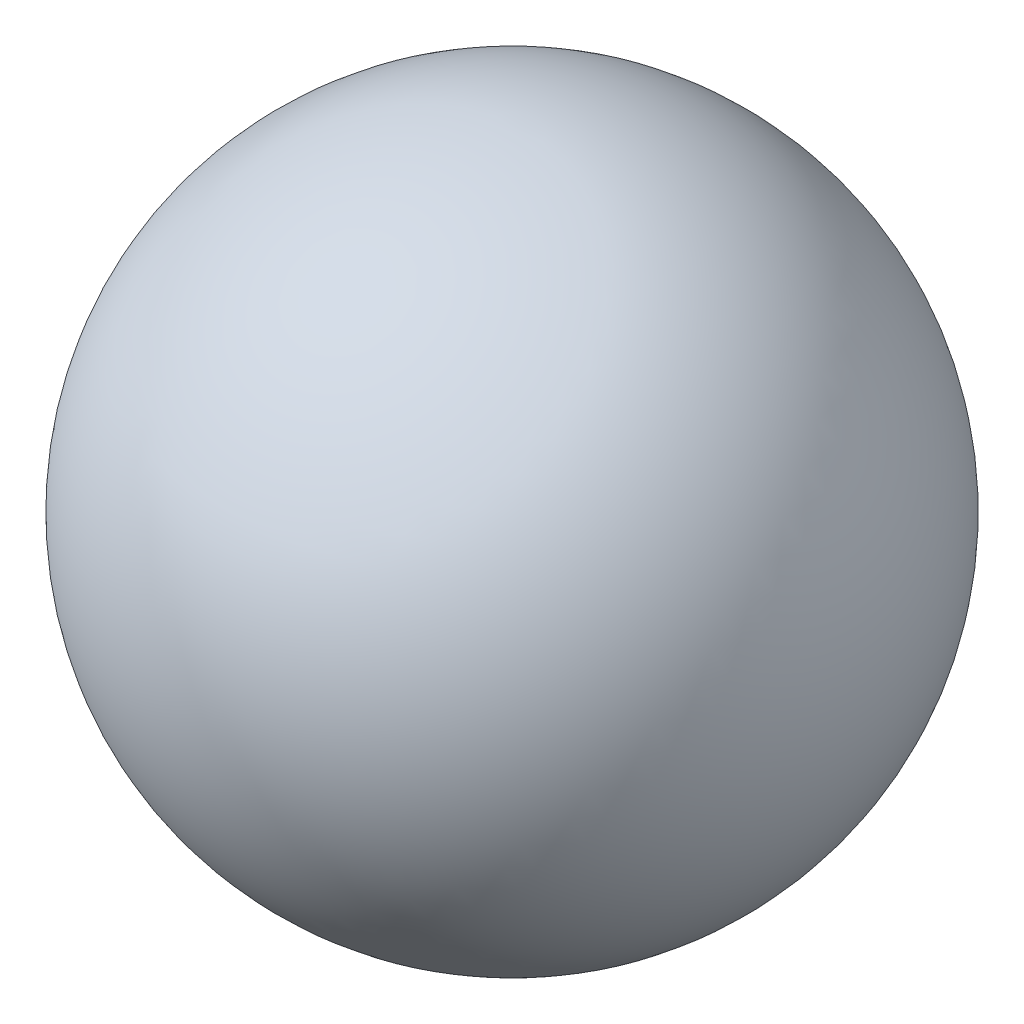
SolidWorks part; units mm, degrees
ref_plane "Front Plane" through (0, 0, 0) normal (0, 0, 1) x (1, 0, 0)
ref_plane "Top Plane" through (0, 0, 0) normal (0, 1, 0) x (1, 0, 0)
ref_plane "Right Plane" through (0, 0, 0) normal (1, 0, 0) x (0, 0, -1)
sketch "Sketch1" plane through (0, 0, 0) normal (0, 0, 1) x (1, 0, 0)
  line L0 (0, 119.8563) -> (0, -119.8563)
  arc A0 (0, -119.8563) -> (0, 119.8563) centre (0, 0) ccw
  point P4 (0, 0)
  dimension "D1" = 239.7125
revolve "Revolve1" add sketch "Sketch1" angle 360 about L0
ref_plane "Plane1" through (0, 119.8563, 0) normal (0, 1, 0) x (1, 0, 0)
sketch "Sketch2" [suppressed] plane through (0, 117.475, 0) normal (0, 1, 0) x (1, 0, 0)
  line L0 (0, 152.4) -> (0, -152.4) construction
  line L1 (-76.2, 0) -> (76.2, 0) construction
  line L2 (0, 247.65) -> (0, -247.65) construction
  circle A0 centre (0, 152.4) radius 95.25
  circle A1 centre (0, -152.4) radius 95.25
  arc A2 (-95.25, 152.4) -> (-95.25, -152.4) centre (-695.325, 0) cw
  arc A3 (95.25, 152.4) -> (95.25, -152.4) centre (695.325, 0) ccw
  circle A4 centre (0, 152.4) radius 90.4875
  circle A5 centre (0, -152.4) radius 90.4875
  arc A6 (-90.4875, 152.4) -> (-90.4875, -152.4) centre (-695.325, 0) cw
  arc A7 (90.4875, 152.4) -> (90.4875, -152.4) centre (695.325, 0) ccw
  point P10 (0, 0)
  dimension "D1" = 190.5
  dimension "D4" = 4.7625
  dimension "D2" = 152.4
  dimension "D3" = 152.4
  dimension "D5" = 495.3
sketch "Sketch3" [suppressed] plane through (0, 117.475, 0) normal (0, 1, 0) x (1, 0, 0)
  arc A0 (95.25, 152.4) -> (95.25, -152.4) centre (695.325, 0) ccw construction
  circle A1 centre (0, -152.4) radius 95.25
  arc A2 (-86.518, -112.5604) -> (86.518, -112.5604) centre (0, -152.4) ccw
  circle A3 centre (0, 152.4) radius 95.25
  arc A4 (86.518, 112.5604) -> (-86.518, 112.5604) centre (0, 152.4) ccw
  arc A5 (-95.25, -152.4) -> (-95.25, 152.4) centre (-695.325, 0) ccw construction
  arc A6 (86.518, 112.5604) -> (86.518, -112.5604) centre (695.325, 0) ccw
  arc A7 (-86.518, -112.5604) -> (-86.518, 112.5604) centre (-695.325, 0) ccw
  arc A8 (90.4875, 152.4) -> (90.4875, -152.4) centre (695.325, 0) ccw construction
  circle A9 centre (0, -152.4) radius 90.4875 construction
  arc A10 (-90.4875, -152.4) -> (-90.4875, 152.4) centre (-695.325, 0) ccw construction
  circle A11 centre (0, 152.4) radius 90.4875 construction
  arc A12 (82.1921, 114.5524) -> (82.1921, -114.5524) centre (695.325, 0) ccw
  arc A13 (-82.1921, -114.5524) -> (82.1921, -114.5524) centre (0, -152.4) ccw
  arc A14 (-82.1921, -114.5524) -> (-82.1921, 114.5524) centre (-695.325, 0) ccw
  arc A15 (82.1921, 114.5524) -> (-82.1921, 114.5524) centre (0, 152.4) ccw
  dimension "D1" = 0
  dimension "D2" = 0
wrap "Wrap2" [suppressed] sketch "Sketch3" source sketch "Sketch3" thickness 1.5875 parameters "D1"=1.5875
